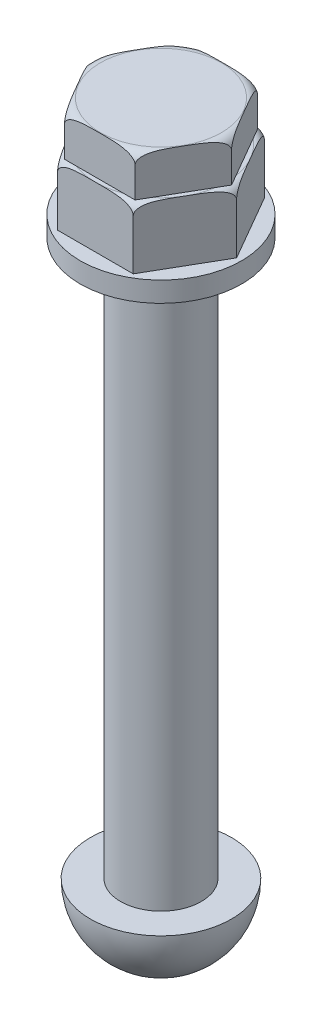
SolidWorks part; units mm, degrees
ref_plane "Front Plane" through (0, 0, 0) normal (0, 0, 1) x (1, 0, 0)
ref_plane "Top Plane" through (0, 0, 0) normal (0, 1, 0) x (1, 0, 0)
ref_plane "Right Plane" through (0, 0, 0) normal (1, 0, 0) x (0, 0, -1)
sketch "Sketch1" plane through (0, 0, 0) normal (0, 0, 1) x (1, 0, 0)
  line L0 (0, 45) -> (0, -79)
  line L1 (8, -65) -> (14, -65)
  line L2 (8, -65) -> (8, 45)
  line L3 (8, 45) -> (0, 45)
  arc A0 (0, -79) -> (14, -65) centre (0, -65) ccw
  point P4 (0, 0)
  dimension "D1" = 14
  dimension "D2" = 110
revolve "Revolve1" add sketch "Sketch1" angle 360 about L0
sketch "Sketch2" plane through (0, 45, 0) normal (0, 1, 0) x (1, 0, 0)
  circle A0 centre (0, 0) radius 16
  dimension "D1" = 16
extrude "Boss-Extrude1" add sketch "Sketch2" along normal blind 4
sketch "Sketch3" plane through (0, 49, 0) normal (0, 1, 0) x (1, 0, 0)
  line L1 (15, 0) -> (7.5, 12.9904)
  line L2 (7.5, 12.9904) -> (-7.5, 12.9904)
  line L3 (-7.5, 12.9904) -> (-15, 0)
  line L4 (-15, 0) -> (-7.5, -12.9904)
  line L5 (-7.5, -12.9904) -> (7.5, -12.9904)
  line L6 (7.5, -12.9904) -> (15, 0)
  circle A0 centre (0, 0) radius 12.9904 construction
  dimension "D1" = 30
extrude "Boss-Extrude2" add sketch "Sketch3" along normal blind 12
sketch "Sketch4" plane through (0, 0, 0) normal (0, 0, 1) x (1, 0, 0)
  line L0 (-11.25, 61) -> (-11.8459, 86.2069)
  line L1 (-15, 61) -> (-7.5, 61) construction
  line L2 (-11.8459, 86.2069) -> (-19.2102, 81.7306)
  line L3 (-19.2102, 81.7306) -> (-15, 77.2181)
  line L4 (-15, 61) -> (-15, 49) construction
  line L5 (-15, 77.2181) -> (-15, 59)
  line L6 (-13, 61) -> (-11.25, 61)
  line L7 (0, 61) -> (0, 88.1923) construction
  line L8 (-7.5, 61) -> (7.5, 61) construction
  arc A0 (-13, 61) -> (-15, 59) centre (-13, 59) ccw
  point P11 (-15, 61)
  dimension "D1" = 2
revolve "Cut-Revolve1" cut sketch "Sketch4" angle 360 about L7
sketch "Sketch5" plane through (0, 61, 0) normal (0, 1, 0) x (1, 0, 0)
  line L1 (14, 0) -> (7, 12.1244)
  line L2 (7, 12.1244) -> (-7, 12.1244)
  line L3 (-7, 12.1244) -> (-14, 0)
  line L4 (-14, 0) -> (-7, -12.1244)
  line L5 (-7, -12.1244) -> (7, -12.1244)
  line L6 (7, -12.1244) -> (14, 0)
  circle A0 centre (0, 0) radius 12.1244 construction
  dimension "D1" = 28
extrude "Boss-Extrude3" add sketch "Sketch5" along normal blind 8
sketch "Sketch7" plane through (0, 0, 0) normal (0, 0, 1) x (1, 0, 0)
  line L0 (-10.4205, 69) -> (-11.4911, 93.3562)
  line L1 (-14, 69) -> (-7, 69) construction
  line L2 (-11.4911, 93.3562) -> (-17.705, 88.3942)
  line L3 (-17.705, 88.3942) -> (-14, 85.3773)
  line L4 (-14, 69) -> (-14, 61) construction
  line L5 (-14, 85.3773) -> (-14, 67)
  line L6 (-12, 69) -> (-10.4205, 69)
  line L13 (0, 69) -> (0, 96.1858) construction
  line L14 (-7, 69) -> (7, 69) construction
  arc A1 (-12, 69) -> (-14, 67) centre (-12, 67) ccw
  point P21 (-14, 61)
  point P24 (-14, 69)
  dimension "D2" = 2
revolve "Cut-Revolve4" cut sketch "Sketch7" angle 360 about L13
